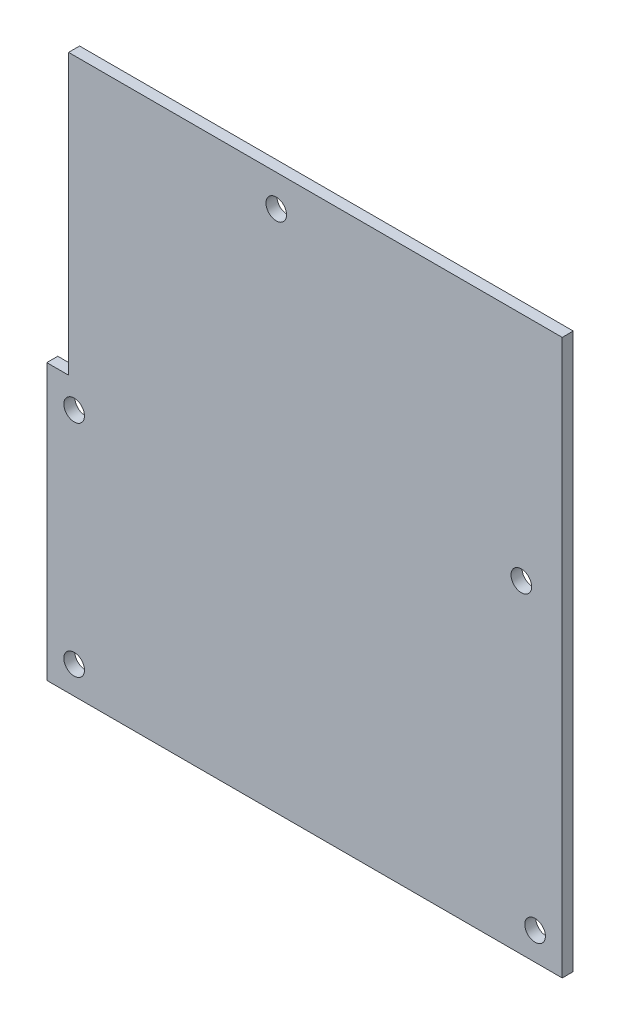
SolidWorks part; units mm, degrees
material "ABS"
ref_plane "Front Plane" through (0, 0, 0) normal (0, 0, 1) x (1, 0, 0)
ref_plane "Top Plane" through (0, 0, 0) normal (0, 1, 0) x (1, 0, 0)
ref_plane "Right Plane" through (0, 0, 0) normal (1, 0, 0) x (0, 0, -1)
sketch "Sketch1" plane through (0, 0, 0) normal (0, 0, 1) x (1, 0, 0)
  line L0 (0, 0) -> (74.93, 0)
  line L1 (0, 0) -> (0, 40.005)
  line L2 (74.93, 0) -> (74.93, 80.645)
  line L3 (0, 40.005) -> (3.175, 40.005)
  line L4 (74.93, 80.645) -> (3.175, 80.645)
  line L5 (3.175, 80.645) -> (3.175, 40.005)
  line L7 (0, 18.796) -> (-1, 18.796)
  line L8 (0, 18.796) -> (0, 30.988)
  line L9 (0, 30.988) -> (-1, 30.988)
  line L10 (-1, 18.796) -> (-1, 30.988)
  line L11 (74.93, 12.192) -> (75.93, 12.192)
  line L12 (74.93, 12.192) -> (74.93, 27.051)
  line L13 (74.93, 27.051) -> (75.93, 27.051)
  line L14 (75.93, 12.192) -> (75.93, 27.051)
  line L15 (3.175, 42.418) -> (2.175, 42.418)
  line L16 (3.175, 42.418) -> (3.175, 60.452)
  line L17 (3.175, 60.452) -> (2.175, 60.452)
  line L18 (2.175, 42.418) -> (2.175, 60.452)
  circle A0 centre (3.984, 4.026) radius 1.5
  circle A1 centre (70.984, 4.026) radius 1.5
  circle A2 centre (3.984, 36.026) radius 1.5
  circle A3 centre (33.3595, 76.026) radius 1.5
  circle A4 centre (68.984, 47.026) radius 1.5
  dimension "D5" = 3
  dimension "D1" = 74.93
  dimension "D2" = 80.645
  dimension "D3" = 40.005
  dimension "D4" = 3.175
  dimension "D6" = 4.026
  dimension "D7" = 3.984
  dimension "D8" = 4.026
  dimension "D9" = 70.984
  dimension "D10" = 3.984
  dimension "D11" = 36.026
  dimension "D12" = 68.984
  dimension "D13" = 47.026
  dimension "D14" = 76.026
  dimension "D15" = 30.1845
  dimension "D16" = 18.796
  dimension "D17" = 12.192
  dimension "D18" = 1
  dimension "D19" = 12.192
  dimension "D20" = 14.859
  dimension "D21" = 1
  dimension "D22" = 2.413
  dimension "D23" = 18.034
  dimension "D24" = 1
extrude "Boss-Extrude1" add sketch "Sketch1" along normal blind 1.6002 contours L4 L5 L3 L1 L0 L2 A4 A3 A2 A1 A0
